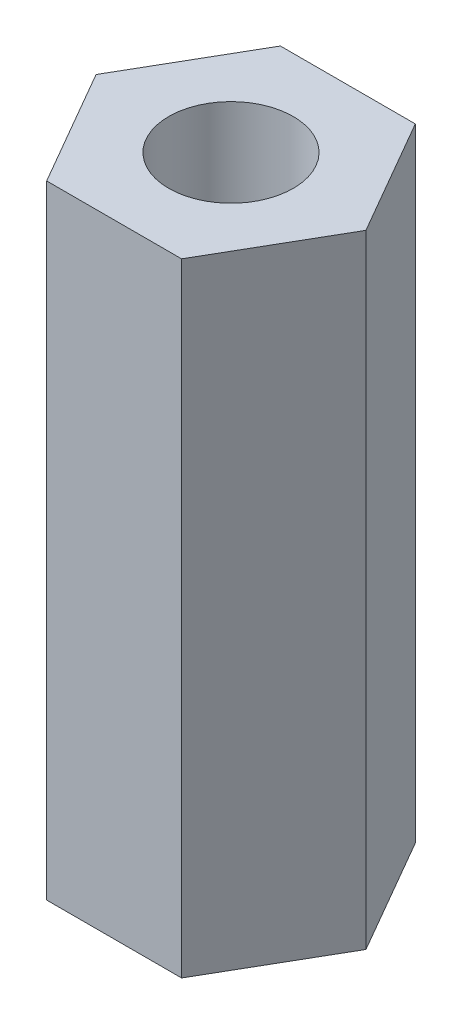
SolidWorks part; units mm, degrees
ref_plane "前视基准面" through (0, 0, 0) normal (0, 0, 1) x (1, 0, 0)
ref_plane "上视基准面" through (0, 0, 0) normal (0, 1, 0) x (1, 0, 0)
ref_plane "右视基准面" through (0, 0, 0) normal (1, 0, 0) x (0, 0, -1)
sketch "草图2" plane through (0, 0, 0) normal (0, 1, 0) x (1, 0, 0)
  line L1 (-1.625, 2.8146) -> (-3.25, 0)
  line L2 (-3.25, 0) -> (-1.625, -2.8146)
  line L3 (-1.625, -2.8146) -> (1.625, -2.8146)
  line L4 (1.625, -2.8146) -> (3.25, 0)
  line L5 (3.25, 0) -> (1.625, 2.8146)
  line L6 (1.625, 2.8146) -> (-1.625, 2.8146)
  circle A0 centre (0, 0) radius 3.25 construction
  circle A1 centre (0, 0) radius 1.5
  dimension "D1" = 3
  dimension "D2" = 6.5
extrude "凸台-拉伸1" add sketch "草图2" along normal blind 15
